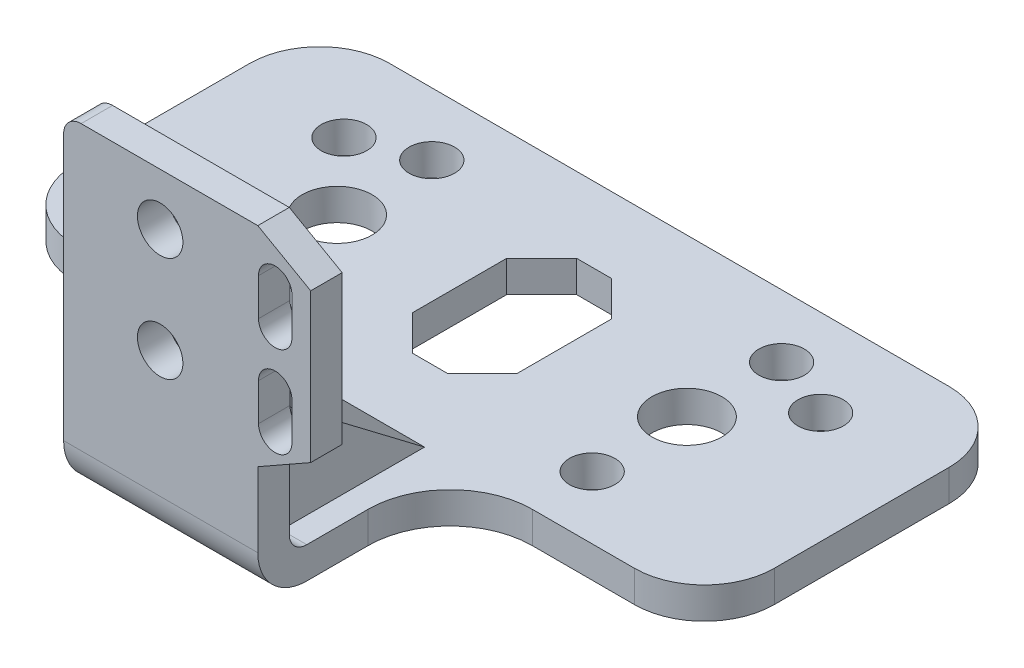
SolidWorks part; units mm, degrees
ref_plane "Front" through (0, 0, 0) normal (0, 0, 1) x (1, 0, 0)
ref_plane "Top" through (0, 0, 0) normal (0, 1, 0) x (1, 0, 0)
ref_plane "Right" through (0, 0, 0) normal (1, 0, 0) x (0, 0, -1)
sketch "Sketch1" plane through (0, 0, 0) normal (1, 0, 0) x (0, 0, -1)
  line L0 (0, 0) -> (0, 45)
  line L1 (0, 45) -> (4.5, 45)
  line L2 (4.5, 45) -> (4.5, 4.5)
  line L3 (4.5, 4.5) -> (75, 4.5)
  line L4 (75, 4.5) -> (75, 0)
  line L5 (75, 0) -> (0, 0)
  dimension "D1" = 4.5
  dimension "D2" = 4.5
  dimension "D3" = 75
  dimension "D4" = 45
extrude "Boss-Extrude1" add sketch "Sketch1" along normal mid plane 100
sketch "Sketch2" plane through (0, 0, 0) normal (0, 1, 0) x (1, 0, 0)
  line L0 (-40, 30) -> (-25.836, 30)
  line L1 (-50, 75) -> (-50, 4.5) construction
  line L2 (50, 75) -> (50, 4.5) construction
  line L4 (-14.0978, 18.2618) -> (-14.0978, 7)
  line L5 (13.6618, 18.2618) -> (13.6618, 7)
  line L7 (50, 75) -> (-50, 75) construction
  line L8 (-2.5, 64.24) -> (2.5, 64.24)
  line L9 (2.5, 64.24) -> (7.5, 59.24)
  line L10 (7.5, 59.24) -> (7.5, 45.76)
  line L11 (7.5, 45.76) -> (2.5, 40.76)
  line L12 (2.5, 40.76) -> (-2.5, 40.76)
  line L13 (-2.5, 40.76) -> (-7.5, 45.76)
  line L14 (-7.5, 45.76) -> (-7.5, 59.24)
  line L15 (-7.5, 59.24) -> (-2.5, 64.24)
  line L16 (-50, 40) -> (-50, 65)
  line L17 (-40, 75) -> (40, 75)
  line L18 (50, 65) -> (50, 40)
  line L19 (25.4, 30) -> (40, 30)
  line L20 (-14.0978, 7) -> (13.6618, 7)
  line L21 (50, 4.5) -> (-50, 4.5) construction
  circle A0 centre (-25, 52.5) radius 5
  circle A1 centre (25, 52.5) radius 5
  circle A2 centre (25, 66.04) radius 3.25
  circle A3 centre (25, 38.96) radius 3.25
  circle A4 centre (34.0726, 62.5509) radius 3.25
  circle A5 centre (-25, 66.04) radius 3.25
  circle A6 centre (-25, 38.96) radius 3.25
  circle A7 centre (-34.0726, 62.5509) radius 3.25
  arc A8 (-40, 75) -> (-50, 65) centre (-40, 65) ccw
  arc A9 (40, 75) -> (50, 65) centre (40, 65) cw
  arc A10 (-40, 30) -> (-50, 40) centre (-40, 40) cw
  arc A11 (40, 30) -> (50, 40) centre (40, 40) ccw
  arc A12 (-14.0978, 18.2618) -> (-25.836, 30) centre (-25.836, 18.2618) ccw
  arc A13 (13.6618, 18.2618) -> (25.4, 30) centre (25.4, 18.2618) cw
  point P43 (-50, 75)
  point P47 (50, 75)
  point P52 (-50, 30)
  point P55 (50, 30)
  point P60 (13.6618, 30)
  point P61 (0, 75)
  dimension "D1" = 45
  dimension "D3" = 22.5
  dimension "D14" = 6.5
  dimension "D19" = 10
  dimension "D20" = 10
  dimension "D21" = 11.7382
  dimension "D22" = 11.7382
  dimension "D2" = 22.5
  dimension "D4" = 50
  dimension "D5" = 25
  dimension "D6" = 225
  dimension "D7" = 225
  dimension "D8" = 225
  dimension "D9" = 225
  dimension "D10" = 15
  dimension "D11" = 5
  dimension "D12" = 23.48
  dimension "D13" = 17.5
  dimension "D15" = 13.54
  dimension "D16" = 13.54
  dimension "D17" = 13.54
  dimension "D18" = 13.54
  dimension "D23" = 10.76
  dimension "D24" = 2.5
  dimension "D25" = 14.164
  dimension "D26" = 14.6
  dimension "D27" = 27.7596
extrude "Cut-Extrude34" cut sketch "Sketch2" against normal through all and the other way through all flip side to cut contours L0 A12 L4 L20 L5 A13 L19 A11 L18 A9 L17 A8 L16 A10 | A6 | A0 | A5 | A7 | L10 L11 L12 L13 L14 L15 L8 L9 | A3 | A1 | A2 | A4
sketch "Sketch4" plane through (0, 0, -7) normal (0, 0, 1) x (1, 0, 0)
  line L0 (-14.0978, 0) -> (-14.0978, 45)
  line L1 (-11.5978, 47.5) -> (13.6618, 47.5)
  line L2 (13.6618, 47.5) -> (21.2228, 43.2094)
  line L3 (21.2228, 43.2094) -> (21.2228, 21.944)
  line L4 (21.2228, 21.944) -> (13.6618, 17.6534)
  line L5 (13.6618, 17.6534) -> (13.6618, 4.5)
  line L6 (13.6618, 4.5) -> (13.6618, 0)
  line L7 (13.6618, 0) -> (-14.0978, 0)
  arc A0 (-11.5978, 47.5) -> (-14.0978, 45) centre (-11.5978, 45) ccw
  dimension "D1" = 2.5
  dimension "D2" = 45
extrude "Boss-Extrude3" add sketch "Sketch4" along normal blind 4.5 contours L0 A0 L1 L2 L3 L4 L5 L6 L7
sketch "Sketch" plane through (0, 0, 0) normal (1, 0, 0) x (0, 0, -1)
  line L0 (7, 21.944) -> (30, 4.5)
  line L1 (30, 4.5) -> (7, 4.5)
  line L2 (4.5, 4.5) -> (75, 4.5) construction
  line L3 (7, 4.5) -> (7, 21.944)
  point P7 (0, 0)
  point P8 (0, 0)
extrude "Support" add sketch "Sketch" along normal mid plane 20
fillet "Fillet3" radius 2.5 1 edges at (11.8309, 4.5, -7)
fillet "Fillet4" radius 7 1 edges at (-0.218, 0, -2.5)
sketch "Sketch6" plane through (0, 0, -2.5) normal (0, 0, 1) x (1, 0, 0)
  line L1 (-14.0978, 7) -> (-14.0978, 45) construction
  circle A0 centre (-0.2978, 40.0831) radius 3.25
  circle A1 centre (-0.2978, 25.0831) radius 3.25
  dimension "D1" = 6.5
  dimension "D2" = 6.5
  dimension "D3" = 15
  dimension "D4" = 13.8
sketch "Sketch7" plane through (0, 0, -2.5) normal (0, 0, 1) x (1, 0, 0)
  line L0 (16.1496, 41.3556) -> (16.1496, 36.0322) construction
  line L1 (18.5396, 41.3556) -> (18.5396, 36.0322)
  line L2 (13.7596, 41.3556) -> (13.7596, 36.0322)
  line L3 (16.1496, 28.3556) -> (16.1496, 23.0322) construction
  line L4 (18.5396, 28.3556) -> (18.5396, 23.0322)
  line L5 (13.7596, 28.3556) -> (13.7596, 23.0322)
  arc A0 (18.5396, 41.3556) -> (13.7596, 41.3556) centre (16.1496, 41.3556) ccw
  arc A1 (13.7596, 36.0322) -> (18.5396, 36.0322) centre (16.1496, 36.0322) ccw
  arc A2 (18.5396, 28.3556) -> (13.7596, 28.3556) centre (16.1496, 28.3556) ccw
  arc A3 (13.7596, 23.0322) -> (18.5396, 23.0322) centre (16.1496, 23.0322) ccw
  point P2 (16.1496, 38.6939)
  point P7 (16.1496, 25.6939)
  dimension "D1" = 4.78
  dimension "D2" = 4.78
  dimension "D3" = 13
extrude "LoadCell_Mount" cut sketch "Sketch6" against normal through all both and the other way through all
extrude "WireHole" cut sketch "Sketch7" against normal blind 5.18
sketch "Sketch9" plane through (0, 0, -7) normal (0, 0, -1) x (-1, 0, 0)
  line L0 (0, 45) -> (0, 4.5) construction
  circle A0 centre (0, 24.75) radius 6.9127
extrude "Cut-Extrude35" cut sketch "Sketch9" along normal blind 10
